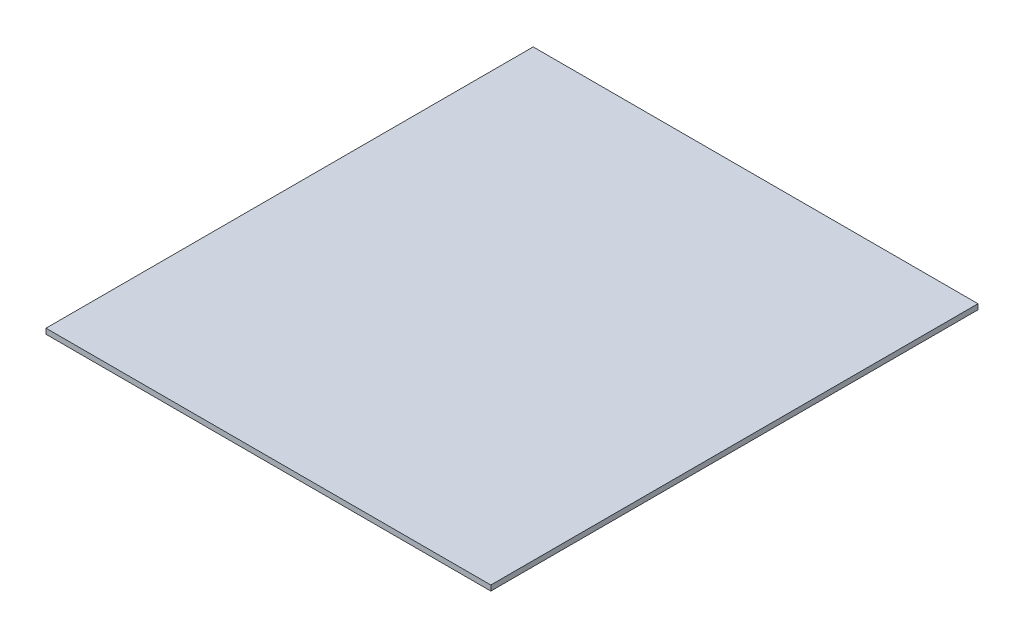
SolidWorks part; units mm, degrees
ref_plane "Front Plane" through (0, 0, 0) normal (0, 0, 1) x (1, 0, 0)
ref_plane "Top Plane" through (0, 0, 0) normal (0, 1, 0) x (1, 0, 0)
ref_plane "Right Plane" through (0, 0, 0) normal (1, 0, 0) x (0, 0, -1)
sketch "Sketch1" plane through (0, 0, 0) normal (0, 1, 0) x (1, 0, 0)
  line L1 (0, 0) -> (133.35, 0)
  line L2 (0, 0) -> (0, 146.05)
  line L3 (0, 146.05) -> (133.35, 146.05)
  line L4 (133.35, 0) -> (133.35, 146.05)
  dimension "D1" = 133.35
  dimension "D2" = 146.05
extrude "Boss-Extrude1" add sketch "Sketch1" along normal blind 1.5875
